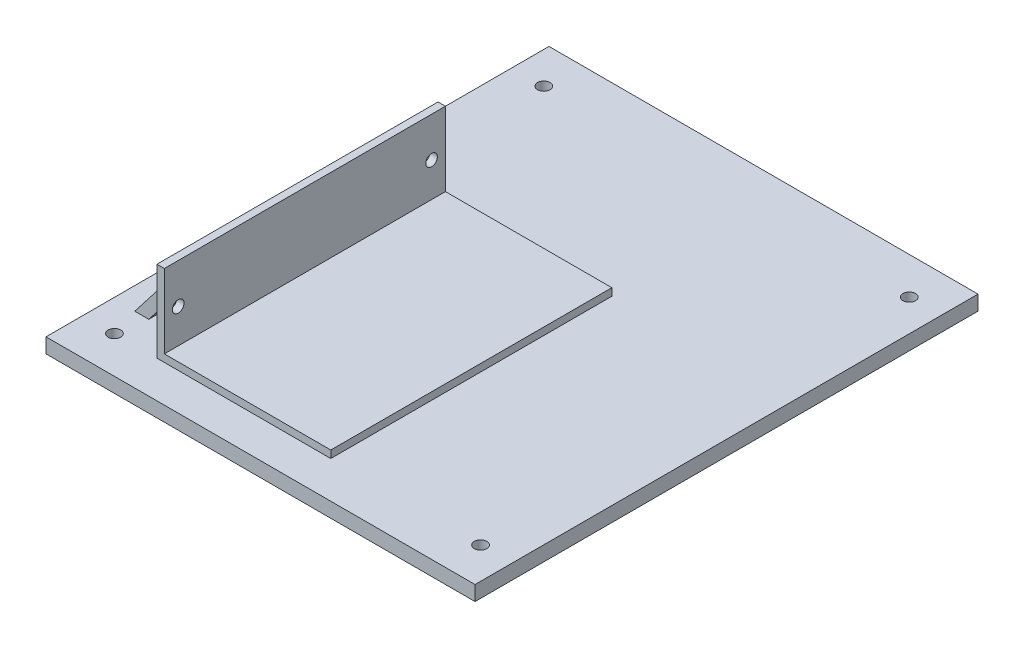
SolidWorks part; units mm, degrees
ref_plane "Front Plane" through (0, 0, 0) normal (0, 0, 1) x (1, 0, 0)
ref_plane "Top Plane" through (0, 0, 0) normal (0, 1, 0) x (1, 0, 0)
ref_plane "Right Plane" through (0, 0, 0) normal (1, 0, 0) x (0, 0, -1)
sketch "Sketch1" plane through (0, 0, 0) normal (0, 0, 1) x (1, 0, 0)
  line L1 (-73.66, -2.54) -> (73.66, -2.54)
  line L2 (-73.66, -2.54) -> (-73.66, 2.54)
  line L3 (-73.66, 2.54) -> (73.66, 2.54)
  line L4 (73.66, -2.54) -> (73.66, 2.54)
  line L5 (-73.66, -2.54) -> (73.66, 2.54) construction
  line L6 (-73.66, 2.54) -> (73.66, -2.54) construction
  point P0 (0, 0)
  dimension "D1" = 147.32
  dimension "D2" = 5.08
extrude "Boss-Extrude1" add sketch "Sketch1" along normal blind 172.72
sketch "Sketch2" plane through (0, 2.54, 0) normal (0, 1, 0) x (1, 0, 0)
  line L0 (73.66, -172.72) -> (-73.66, -172.72) construction
  line L1 (-73.66, -172.72) -> (-73.66, 0) construction
  line L2 (73.66, -172.72) -> (73.66, 0) construction
  line L3 (73.66, 0) -> (-73.66, 0) construction
  circle A0 centre (62.738, -12.7) radius 2.159
  circle A1 centre (-62.865, -160.02) radius 2.159
  circle A2 centre (62.865, -160.02) radius 2.159
  circle A3 centre (-62.738, -12.7) radius 2.159
  dimension "D1" = 4.318
  dimension "D7" = 4.318
  dimension "D2" = 10.922
  dimension "D3" = 12.7
  dimension "D4" = 12.7
  dimension "D5" = 10.795
  dimension "D6" = 10.795
  dimension "D8" = 12.7
  dimension "D9" = 10.922
  dimension "D10" = 12.7
extrude "Cut-Extrude1" cut sketch "Sketch2" against normal through all
sketch "Sketch3" plane through (0, 2.54, 0) normal (0, 1, 0) x (1, 0, 0)
  line L1 (-48.26, -63.5) -> (11.43, -63.5)
  line L2 (-48.26, -63.5) -> (-48.26, -160.02)
  line L3 (-48.26, -160.02) -> (11.43, -160.02)
  line L4 (11.43, -63.5) -> (11.43, -160.02)
  line L6 (-73.66, -172.72) -> (-73.66, 0) construction
  line L7 (73.66, -172.72) -> (-73.66, -172.72) construction
  dimension "D1" = 96.52
  dimension "D2" = 12.7
  dimension "D3" = 59.69
  dimension "D4" = 25.4
extrude "Boss-Extrude2" add sketch "Sketch3" along normal blind 2.54
sketch "Sketch4" plane through (0, 5.08, 0) normal (0, 1, 0) x (1, 0, 0)
  line L0 (-48.26, -160.02) -> (11.43, -160.02) construction
  line L1 (-48.26, -63.5) -> (-45.72, -63.5)
  line L2 (-48.26, -63.5) -> (-48.26, -160.02)
  line L3 (-48.26, -160.02) -> (-45.72, -160.02)
  line L4 (-45.72, -63.5) -> (-45.72, -160.02)
  dimension "D1" = 2.54
extrude "Boss-Extrude3" add sketch "Sketch4" along normal blind 25.4
sketch "Sketch5" plane through (-48.26, 0, 0) normal (-1, 0, 0) x (0, 0, 1)
  line L0 (63.5, 2.54) -> (160.02, 2.54) construction
  line L1 (73.66, 2.54) -> (149.86, 2.54)
  line L2 (73.66, 2.54) -> (73.66, 25.4)
  line L3 (73.66, 25.4) -> (149.86, 25.4)
  line L4 (149.86, 2.54) -> (149.86, 25.4)
  line L5 (63.5, 30.48) -> (63.5, 2.54) construction
  line L6 (160.02, 30.48) -> (160.02, 2.54) construction
  line L7 (63.5, 30.48) -> (160.02, 30.48) construction
  point P10 (160.02, 16.51)
  dimension "D1" = 10.16
  dimension "D2" = 10.16
  dimension "D3" = 5.08
extrude "Boss-Extrude4" add sketch "Sketch5" along normal blind 17.78
sketch "Sketch6" plane through (0, 0, 149.86) normal (0, 0, 1) x (1, 0, 0)
  line L0 (-66.04, 2.54) -> (-48.26, 25.4)
  line L1 (-66.04, 2.54) -> (-66.04, 25.4)
  line L2 (-66.04, 25.4) -> (-48.26, 25.4)
  line L3 (-61.2133, 2.54) -> (-48.26, 19.1942)
  line L4 (-66.04, 2.54) -> (-48.26, 2.54) construction
  line L5 (-48.26, 30.48) -> (-48.26, 2.54) construction
  line L6 (-48.26, 19.1942) -> (-48.26, 2.54)
  line L7 (-48.26, 2.54) -> (-61.2133, 2.54)
  dimension "D1" = 3.81
extrude "Cut-Extrude2" cut sketch "Sketch6" against normal through all
sketch "Sketch7" plane through (-45.72, 0, 0) normal (1, 0, 0) x (0, 0, -1)
  line L0 (-111.76, 16.83) -> (-111.76, 5.08) construction
  line L2 (-155.26, 16.83) -> (-68.26, 16.83) construction
  line L3 (-160.02, 5.08) -> (-63.5, 5.08) construction
  circle A0 centre (-155.26, 16.83) radius 2
  circle A1 centre (-68.26, 16.83) radius 2
  point P9 (-111.76, 16.83)
  dimension "D3" = 4
  dimension "D4" = 4
  dimension "D1" = 11.75
  dimension "D2" = 87
extrude "Cut-Extrude3" cut sketch "Sketch7" against normal through all
